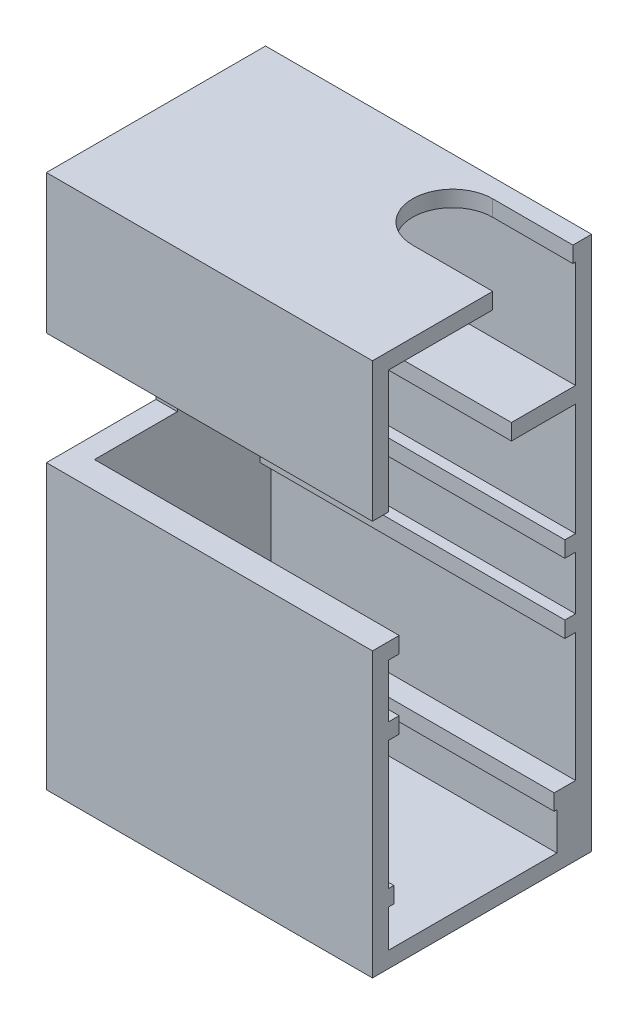
SolidWorks part; units mm, degrees
ref_plane "Plan de face" through (0, 0, 0) normal (0, 0, 1) x (1, 0, 0)
ref_plane "Plan de dessus" through (0, 0, 0) normal (0, 1, 0) x (1, 0, 0)
ref_plane "Plan de droite" through (0, 0, 0) normal (1, 0, 0) x (0, 0, -1)
sketch "Esquisse1" plane through (0, 0, 0) normal (0, 1, 0) x (1, 0, 0)
  line L1 (-30.5, -20.5) -> (30.5, -20.5)
  line L2 (-30.5, -20.5) -> (-30.5, 20.5)
  line L3 (-30.5, 20.5) -> (30.5, 20.5)
  line L4 (30.5, -20.5) -> (30.5, 20.5)
  line L5 (-30.5, -20.5) -> (30.5, 20.5) construction
  line L6 (-30.5, 20.5) -> (30.5, -20.5) construction
  point P0 (0, 0)
  dimension "D1" = 61
  dimension "D2" = 41
extrude "Boss.-Extru.1" add sketch "Esquisse1" along normal blind 100
sketch "Esquisse3" plane through (30.5, 0, 0) normal (1, 0, 0) x (0, 0, -1)
  line L0 (-20.5, 100) -> (20.5, 0) construction
  line L1 (17.5, 13) -> (17.5, 97)
  line L2 (14, 3) -> (-17.5, 3)
  line L4 (17.5, 97) -> (-17.5, 97)
  line L5 (-17.5, 3) -> (-17.5, 97)
  line L6 (17.5, 3) -> (-17.5, 97) construction
  line L7 (17.5, 97) -> (-17.5, 3) construction
  line L8 (-20.5, 100) -> (20.5, 100) construction
  line L14 (17.5, 13) -> (14, 13)
  line L15 (14, 3) -> (14, 13)
  point P4 (0, 50)
  point P5 (0, 50)
  dimension "D1" = 3
  dimension "D3" = 3.5
  dimension "D4" = 10
extrude "Enlèv. mat.-Extru.1" cut sketch "Esquisse3" against normal blind 57 contours L4 L5 L2 L15 L14 L1
sketch "Esquisse6" plane through (0, 0, -20.5) normal (0, 0, -1) x (-1, 0, 0)
  line L0 (-30.5, 100) -> (-30.5, 0) construction
  line L1 (-30.5, 10) -> (27.5, 10)
  line L2 (-30.5, 10) -> (-30.5, 13)
  line L3 (-30.5, 13) -> (27.5, 13)
  line L4 (27.5, 10) -> (27.5, 13)
  line L5 (30.5, 100) -> (30.5, 0) construction
  line L6 (-30.5, 0) -> (30.5, 0) construction
  dimension "D1" = 3
  dimension "D2" = 3
  dimension "D3" = 10
extrude "Boss.-Extru.2" add sketch "Esquisse6" against normal blind 4
mirror "Symétrie1" about plane through (0, 0, 0) normal (0, 0, 1) of "Boss.-Extru.2"
sketch "Esquisse7" plane through (-30.5, 0, 0) normal (-1, 0, 0) x (0, 0, 1)
  line L0 (-20.5, 100) -> (-20.5, 0) construction
  line L1 (-17.5, 10) -> (17.5, 10)
  line L2 (-17.5, 10) -> (-17.5, 13)
  line L3 (-17.5, 13) -> (17.5, 13)
  line L4 (17.5, 10) -> (17.5, 13)
  line L5 (-20.5, 0) -> (20.5, 0) construction
  line L6 (20.5, 100) -> (20.5, 0) construction
  dimension "D1" = 3
  dimension "D2" = 3
  dimension "D3" = 10
  dimension "D4" = 3
extrude "Boss.-Extru.3" add sketch "Esquisse7" against normal blind 6
sketch "Esquisse11" plane through (0, 0, -20.5) normal (0, 0, -1) x (-1, 0, 0)
  line L0 (-30.5, 100) -> (-30.5, 0) construction
  line L1 (-30.5, 10) -> (27.5, 10)
  line L2 (-30.5, 10) -> (-30.5, 13)
  line L3 (-30.5, 13) -> (27.5, 13)
  line L4 (27.5, 10) -> (27.5, 13)
  line L5 (30.5, 100) -> (30.5, 0) construction
  line L6 (-30.5, 0) -> (30.5, 0) construction
  dimension "D1" = 0
  dimension "D2" = 3
  dimension "D3" = 3
  dimension "D4" = 10
extrude "Boss.-Extru.4" add sketch "Esquisse11" against normal blind 7
sketch "Esquisse12" plane through (0, 0, -20.5) normal (0, 0, -1) x (-1, 0, 0)
  line L0 (-30.5, 100) -> (-30.5, 0) construction
  line L1 (-30.5, 50) -> (29.0466, 50)
  line L2 (-30.5, 50) -> (-30.5, 53)
  line L3 (-30.5, 53) -> (29.0466, 53)
  line L4 (29.0466, 50) -> (29.0466, 53)
  line L5 (-30.5, 0) -> (30.5, 0) construction
  dimension "D1" = 3
  dimension "D2" = 50
extrude "Boss.-Extru.5" add sketch "Esquisse12" against normal blind 5
mirror "Symétrie2" about plane through (0, 0, 0) normal (0, 0, 1) of "Boss.-Extru.5"
pattern_linear "Répétition linéaire1" count 2 spacing 13 along (0, -1, 0) of "Symétrie2", "Boss.-Extru.5"
sketch "Esquisse13" plane through (0, 0, 20.5) normal (0, 0, 1) x (1, 0, 0)
  line L0 (-30.5, 100) -> (-30.5, 0) construction
  line L1 (-27.5, 83) -> (-12.5, 83)
  line L2 (-27.5, 83) -> (-27.5, 80)
  line L3 (-27.5, 80) -> (-12.5, 80)
  line L4 (-12.5, 83) -> (-12.5, 80)
  line L5 (-30.5, 100) -> (30.5, 100) construction
  dimension "D1" = 3
  dimension "D2" = 3
  dimension "D3" = 15
  dimension "D4" = 17
extrude "Boss.-Extru.6" add sketch "Esquisse13" against normal blind 5 contours L3 L4 L1 L2
pattern_linear "Répétition linéaire3" count 2 spacing 4 along (0, 1, 0) of "Boss.-Extru.6"
sketch "Esquisse14" plane through (0, 0, -20.5) normal (0, 0, -1) x (-1, 0, 0)
  line L0 (30.5, 100) -> (30.5, 0) construction
  line L1 (27.5, 80) -> (12.5, 80)
  line L2 (27.5, 80) -> (27.5, 87)
  line L3 (27.5, 87) -> (12.5, 87)
  line L4 (12.5, 80) -> (12.5, 87)
  line L6 (-30.5, 100) -> (30.5, 100) construction
  dimension "D1" = 15
  dimension "D2" = 3
  dimension "D3" = 7
  dimension "D4" = 20
extrude "Boss.-Extru.7" add sketch "Esquisse14" against normal blind 16
sketch "Esquisse15" plane through (-12.5, 0, 0) normal (1, 0, 0) x (0, 0, -1)
  line L0 (4.5, 80) -> (4.5, 87) construction
  line L1 (3.5, 83) -> (5.5, 83)
  line L2 (3.5, 83) -> (3.5, 84)
  line L3 (3.5, 84) -> (5.5, 84)
  line L4 (5.5, 83) -> (5.5, 84)
  line L5 (3.5, 83) -> (5.5, 84) construction
  line L6 (3.5, 84) -> (5.5, 83) construction
  point P0 (4.5, 83.5)
  dimension "D1" = 1
  dimension "D2" = 2
extrude "Enlèv. mat.-Extru.2" cut sketch "Esquisse15" against normal up to surface (14 mm away) up to face at (-26.5, 60.6875, 2.75)
sketch "Esquisse16" plane through (0, 100, 0) normal (0, 1, 0) x (1, 0, 0)
  line L1 (30.5, 20.5) -> (-30.5, 20.5) construction
  line L2 (30.5, -20.5) -> (30.5, 20.5) construction
  line L3 (15.5, 2) -> (30.5, 2)
  line L4 (15.5, 17) -> (30.5, 17)
  line L5 (30.5, 2) -> (30.5, 17)
  arc A0 (15.5, 17) -> (15.5, 2) centre (15.5, 9.5) ccw
  dimension "D1" = 15
  dimension "D2" = 15
  dimension "D3" = 11
extrude "Enlèv. mat.-Extru.3" cut sketch "Esquisse16" against normal blind 15
sketch "Esquisse17" plane through (0, 0, -20.5) normal (0, 0, -1) x (-1, 0, 0)
  line L0 (-30.5, 100) -> (-30.5, 0) construction
  line L1 (-30.5, 74) -> (29.4544, 74)
  line L2 (-30.5, 74) -> (-30.5, 77)
  line L3 (-30.5, 77) -> (29.4544, 77)
  line L4 (29.4544, 74) -> (29.4544, 77)
  line L5 (-30.5, 100) -> (30.5, 100) construction
  dimension "D1" = 3
  dimension "D2" = 23
extrude "Boss.-Extru.8" add sketch "Esquisse17" against normal blind 15
sketch "Esquisse18" plane through (30.5, 0, 0) normal (1, 0, 0) x (0, 0, -1)
  line L0 (-20.5, 100) -> (-20.5, 0) construction
  line L1 (-20.5, 74) -> (0, 74)
  line L2 (-20.5, 74) -> (-20.5, 53)
  line L3 (-20.5, 53) -> (0, 53)
  line L4 (0, 74) -> (0, 53)
  line L5 (0, 0) -> (0, 100) construction
  line L6 (-20.5, 100) -> (2, 100) construction
  line L7 (15.5, 53) -> (17.5, 53) construction
  line L9 (5.5, 74) -> (17.5, 74) construction
extrude "Enlèv. mat.-Extru.4" cut sketch "Esquisse18" against normal through all
